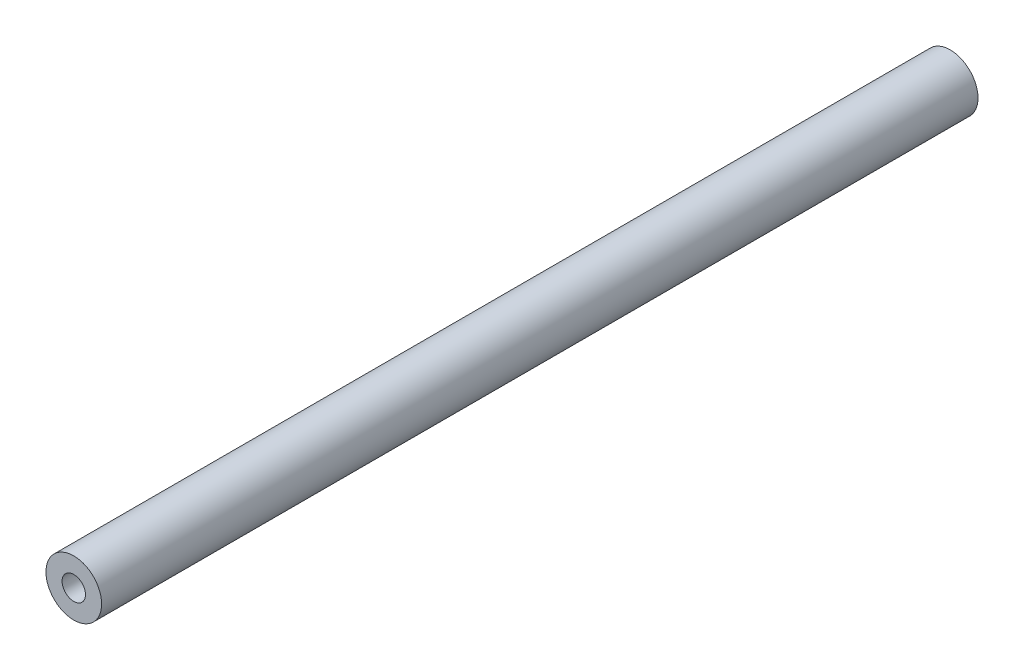
SolidWorks part; units mm, degrees
ref_plane "Alzado" through (0, 0, 0) normal (0, 0, 1) x (1, 0, 0)
ref_plane "Planta" through (0, 0, 0) normal (0, 1, 0) x (1, 0, 0)
ref_plane "Vista lateral" through (0, 0, 0) normal (1, 0, 0) x (0, 0, -1)
sketch "Croquis1" plane through (0, 0, 0) normal (0, 0, 1) x (1, 0, 0)
  circle A0 centre (0, 0) radius 4.7625
  circle A1 centre (0, 0) radius 2
  dimension "D1" = 9.525
  dimension "D2" = 4
extrude "Saliente-Extruir1" add sketch "Croquis1" along normal blind 150
